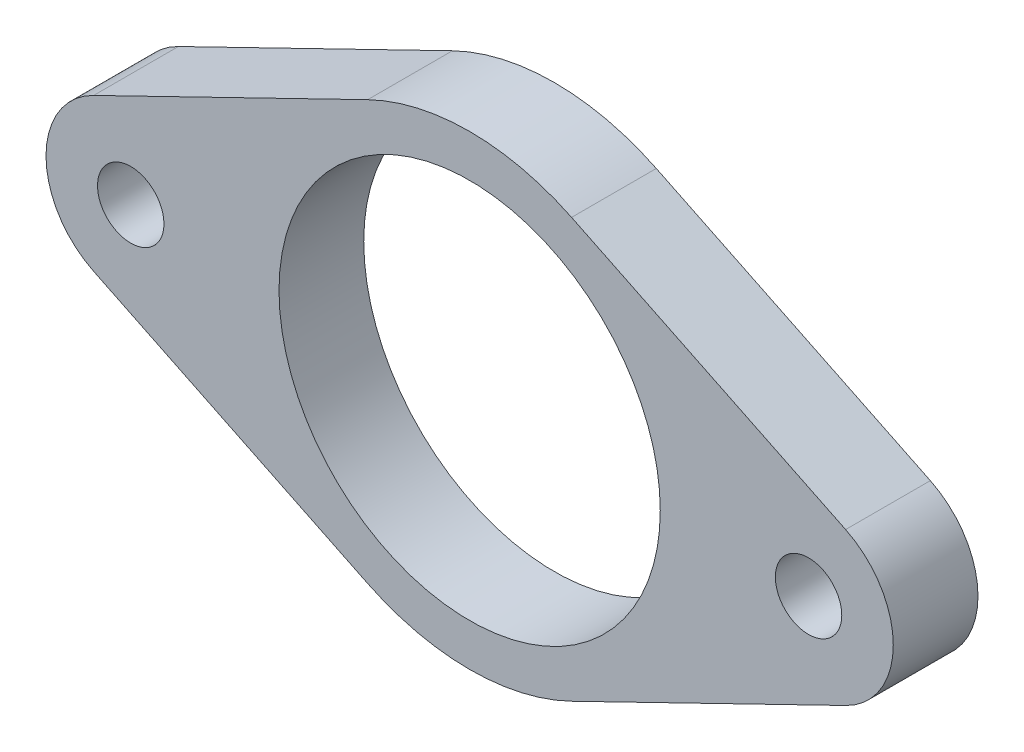
SolidWorks part; units mm, degrees
ref_plane "Front Plane" through (0, 0, 0) normal (0, 0, 1) x (1, 0, 0)
ref_plane "Top Plane" through (0, 0, 0) normal (0, 1, 0) x (1, 0, 0)
ref_plane "Right Plane" through (0, 0, 0) normal (1, 0, 0) x (0, 0, -1)
sketch "Sketch2" plane through (0, 0, 0) normal (0, 0, 1) x (1, 0, 0)
  line L0 (7.6398, 15.7026) -> (28.1781, 5.71)
  line L1 (-7.6398, 15.7026) -> (-28.1781, 5.71)
  line L3 (-7.6398, -15.7026) -> (-28.1781, -5.71)
  line L4 (7.6398, -15.7026) -> (28.1781, -5.71)
  arc A0 (7.6398, 15.7026) -> (-7.6398, 15.7026) centre (0, 0) ccw
  arc A2 (-28.1781, 5.71) -> (-28.1781, -5.71) centre (-25.4, 0) ccw
  circle A3 centre (0, 0) radius 14.2875
  arc A4 (28.1781, 5.71) -> (28.1781, -5.71) centre (25.4, 0) cw
  arc A5 (7.6398, -15.7026) -> (-7.6398, -15.7026) centre (0, 0) cw
  circle A6 centre (-25.4, 0) radius 2.4892
  circle A7 centre (25.4, 0) radius 2.4892
  point P16 (7.7854, -15.6309)
  point P17 (7.9699, -15.5377)
  dimension "D1" = 28.575
  dimension "D2" = 4.9784
  dimension "D3" = 17.4625
  dimension "D4" = 6.35
  dimension "D5" = 50.8
extrude "Boss-Extrude1" add sketch "Sketch2" along normal blind 6.35
